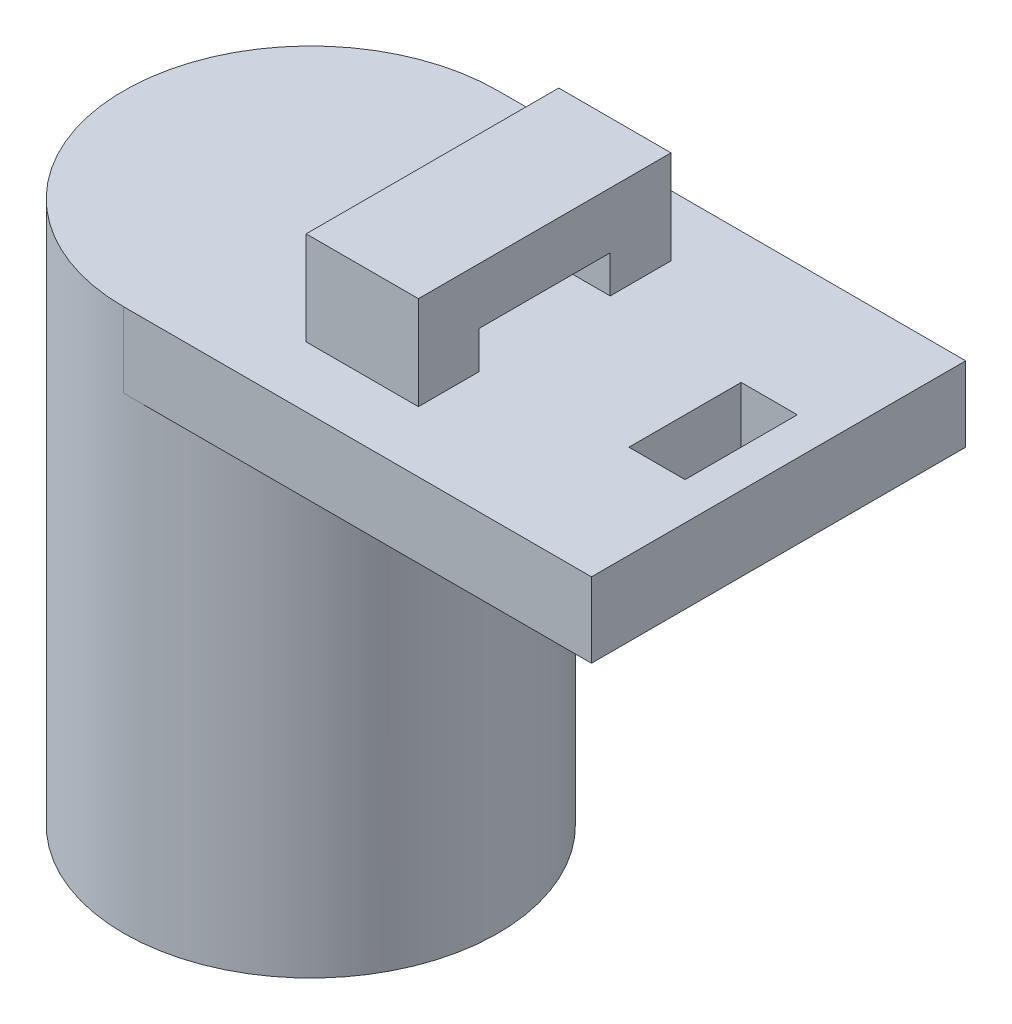
SolidWorks part; units mm, degrees
material "Epoxy, Unfilled"
ref_plane "Front Plane" through (0, 0, 0) normal (0, 0, 1) x (1, 0, 0)
ref_plane "Top Plane" through (0, 0, 0) normal (0, 1, 0) x (1, 0, 0)
ref_plane "Right Plane" through (0, 0, 0) normal (1, 0, 0) x (0, 0, -1)
sketch "Sketch1" plane through (0, 0, 0) normal (0, 1, 0) x (1, 0, 0)
  circle A0 centre (0, 0) radius 6.5
  circle A1 centre (0, 0) radius 10
  dimension "D1" = 13
  dimension "D2" = 20
extrude "Boss-Extrude1" add sketch "Sketch1" along normal blind 25
sketch "Sketch2" plane through (0, 25, 0) normal (0, 1, 0) x (1, 0, 0)
  line L1 (0, 10) -> (25, 10)
  line L3 (0, -10) -> (25, -10)
  line L4 (25, 10) -> (25, -10)
  arc A0 (0, 10) -> (0, -10) centre (0, 0) ccw
  circle A1 centre (0, 0) radius 10 construction
  dimension "D1" = 25
extrude "Boss-Extrude2" add sketch "Sketch2" along normal blind 4
sketch "Sketch3" plane through (0, 29, 0) normal (0, 1, 0) x (1, 0, 0)
  line L0 (0, 0) -> (25.7859, 0) construction
  line L1 (6.5, 6.75) -> (12.5, 6.75)
  line L2 (6.5, 6.75) -> (6.5, -6.75)
  line L3 (6.5, -6.75) -> (12.5, -6.75)
  line L4 (12.5, 6.75) -> (12.5, -6.75)
  dimension "D1" = 13.5
  dimension "D2" = 6.5
  dimension "D3" = 6
extrude "Boss-Extrude3" add sketch "Sketch3" along normal blind 5
sketch "Sketch4" plane through (12.5, 0, 0) normal (1, 0, 0) x (0, 0, -1)
  line L0 (0, 29) -> (0, 34.5993) construction
  line L1 (-6.75, 29) -> (6.75, 29) construction
  line L4 (-3.5, 31) -> (3.5, 31)
  line L5 (-3.5, 31) -> (-3.5, 29)
  line L6 (-3.5, 29) -> (3.5, 29)
  line L7 (3.5, 31) -> (3.5, 29)
  dimension "D1" = 7
  dimension "D2" = 2
extrude "Cut-Extrude1" cut sketch "Sketch4" against normal blind 12
sketch "Sketch5" plane through (0, 29, 0) normal (0, 1, 0) x (1, 0, 0)
  line L0 (0, 0) -> (28.4421, 0) construction
  line L1 (20, -3) -> (23, -3)
  line L2 (20, -3) -> (20, 3)
  line L3 (20, 3) -> (23, 3)
  line L4 (23, -3) -> (23, 3)
  line L5 (25, -10) -> (25, 10) construction
  dimension "D1" = 3
  dimension "D2" = 2
  dimension "D3" = 5
  dimension "D4" = 3
extrude "Cut-Extrude2" cut sketch "Sketch5" against normal blind 12
